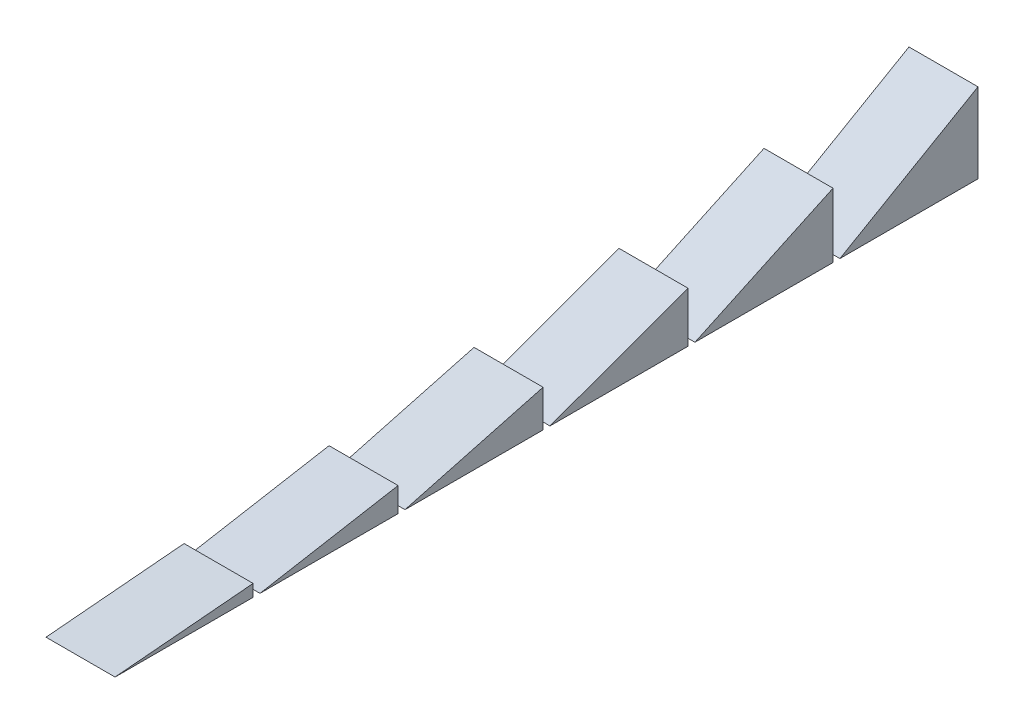
SolidWorks part; units mm, degrees
ref_plane "Front Plane" through (0, 0, 0) normal (0, 0, 1) x (1, 0, 0)
ref_plane "Top Plane" through (0, 0, 0) normal (0, 1, 0) x (1, 0, 0)
ref_plane "Right Plane" through (0, 0, 0) normal (1, 0, 0) x (0, 0, -1)
sketch "Sketch1" plane through (0, 0, 0) normal (1, 0, 0) x (0, 0, -1)
  line L0 (0, 0) -> (50.8, 0)
  line L1 (50.8, 0) -> (50.8, 4.4444)
  line L2 (50.8, 4.4444) -> (0, 0)
  line L3 (53.34, 0) -> (104.14, 0)
  line L4 (104.14, 0) -> (104.14, 8.9574)
  line L5 (104.14, 8.9574) -> (53.34, 0)
  line L6 (106.68, 0) -> (157.48, 0)
  line L7 (157.48, 0) -> (157.48, 13.6118)
  line L8 (157.48, 13.6118) -> (106.68, 0)
  line L9 (160.02, 0) -> (210.82, 0)
  line L10 (210.82, 0) -> (210.82, 18.4897)
  line L11 (210.82, 18.4897) -> (160.02, 0)
  line L12 (213.36, 0) -> (264.16, 0)
  line L13 (264.16, 0) -> (264.16, 23.6884)
  line L14 (264.16, 23.6884) -> (213.36, 0)
  line L15 (266.7, 0) -> (317.5, 0)
  line L16 (317.5, 0) -> (317.5, 29.3294)
  line L17 (317.5, 29.3294) -> (266.7, 0)
  dimension "D1" = 50.8
  dimension "D2" = 5
  dimension "D3" = 50.8
  dimension "D4" = 2.54
  dimension "D5" = 2.54
  dimension "D6" = 10
  dimension "D7" = 50.8
  dimension "D8" = 2.54
  dimension "D9" = 15
  dimension "D10" = 50.8
  dimension "D11" = 20
  dimension "D12" = 2.54
  dimension "D13" = 2.54
  dimension "D14" = 50.8
  dimension "D15" = 50.8
  dimension "D16" = 25
  dimension "D17" = 30
extrude "Boss-Extrude1" add sketch "Sketch1" along normal blind 25.4
